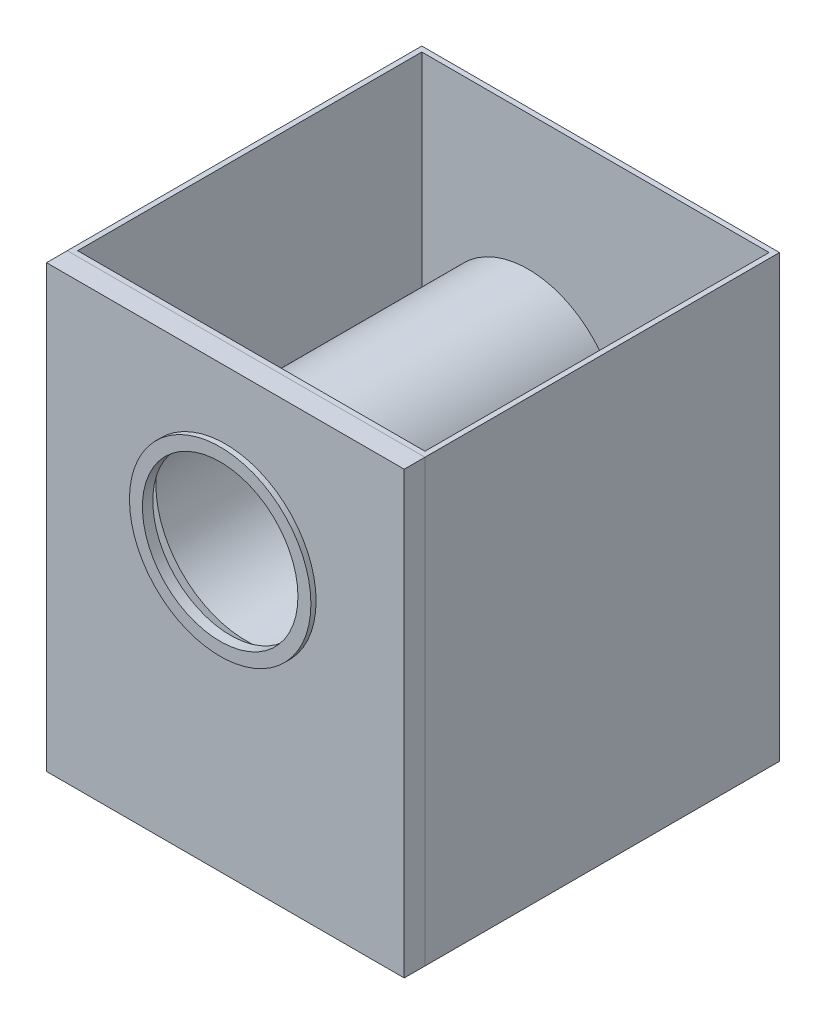
SolidWorks part; units mm, degrees
ref_plane "Front Plane" through (0, 0, 0) normal (0, 0, 1) x (1, 0, 0)
ref_plane "Top Plane" through (0, 0, 0) normal (0, 1, 0) x (1, 0, 0)
ref_plane "Right Plane" through (0, 0, 0) normal (1, 0, 0) x (0, 0, -1)
ref_plane "Plane1" through (0, -890, 0) normal (0, -1, 0) x (-1, 0, 0)
sketch "Sketch2" plane through (0, -890, 0) normal (0, -1, 0) x (-1, 0, 0)
  line L3 (-345, 361.95) -> (345, 361.95)
  line L4 (-345, 361.95) -> (-345, -321.95)
  line L5 (-345, -321.95) -> (345, -321.95)
  line L6 (345, 361.95) -> (345, -321.95)
  dimension "D1" = 683.9
  dimension "D2" = 690
extrude "Boss-Extrude2" add sketch "Sketch2" against normal blind 10
sketch "Sketch3" plane through (0, -890, 0) normal (0, -1, 0) x (-1, 0, 0)
  line L0 (335, 351.95) -> (335, -311.95)
  line L1 (345, 361.95) -> (-345, 361.95)
  line L2 (345, 361.95) -> (345, -321.95)
  line L3 (345, -321.95) -> (-345, -321.95)
  line L4 (-345, 361.95) -> (-345, -321.95)
  line L5 (335, -311.95) -> (-335, -311.95)
  line L6 (-335, 351.95) -> (-335, -311.95)
  line L7 (335, 351.95) -> (-335, 351.95)
  dimension "D1" = 683.9
  dimension "D2" = 690
  dimension "D3" = 10
extrude "Boss-Extrude3" add sketch "Sketch3" against normal blind 850
ref_plane "Plane2" through (0, 0, 321.95) normal (0, 0, 1) x (1, 0, 0)
sketch "Sketch4" plane through (0, 0, 321.95) normal (0, 0, 1) x (1, 0, 0)
  line L0 (0, -890) -> (0, -595.2) construction
  line L1 (345, -890) -> (-345, -890) construction
  line L2 (0, -40) -> (0, -100) construction
  line L3 (345, -40) -> (-345, -40) construction
  line L4 (0, -100) -> (0, -80) construction
  line L5 (-345, -80) -> (-345, -555.2) construction
  line L6 (-345, -40) -> (-345, -890) construction
  line L7 (-345, -317.6) -> (-305, -317.6) construction
  line L8 (345, -317.6) -> (305, -317.6) construction
  line L9 (345, -40) -> (345, -890) construction
  line L10 (0, -595.2) -> (0, -345.2) construction
  circle A0 centre (0, -345.2) radius 175
  dimension "D3" = 350
  dimension "D1" = 294.8
  dimension "D2" = 60
extrude "Cut-Extrude7" cut sketch "Sketch4" against normal blind 30
ref_plane "Plane3" through (0, 0, 361.95) normal (0, 0, 1) x (1, 0, 0)
sketch "Sketch5" plane through (0, 0, 361.95) normal (0, 0, 1) x (1, 0, 0)
  line L1 (-345, -40) -> (345, -40)
  line L2 (-345, -40) -> (-345, -890)
  line L3 (-345, -890) -> (345, -890)
  line L4 (345, -40) -> (345, -890)
  dimension "D1" = 850
  dimension "D2" = 690
extrude "Boss-Extrude4" add sketch "Sketch5" against normal blind 10 separate body
sketch "Sketch6" plane through (0, 0, 361.95) normal (0, 0, 1) x (1, 0, 0)
  circle A1 centre (0, -345.2) radius 175
  circle A2 centre (0, -345.2) radius 150
  dimension "D1" = 350
  dimension "D2" = 300
sketch "Sketch7" plane through (0, 0, 361.95) normal (0, 0, 1) x (1, 0, 0)
  line L1 (345, -40) -> (-345, -40)
  line L2 (345, -40) -> (345, -890)
  line L3 (345, -890) -> (-345, -890)
  line L4 (-345, -40) -> (-345, -890)
  line L6 (345, -890) -> (-345, -890) construction
  line L7 (-345, -40) -> (-345, -890) construction
  line L8 (344, -41) -> (344, -889)
  line L9 (344, -889) -> (-344, -889)
  line L10 (-344, -41) -> (-344, -889)
  line L11 (344, -41) -> (-344, -41)
  dimension "D1" = 850
  dimension "D2" = 690
  dimension "D3" = 1
extrude "Boss-Extrude5" add sketch "Sketch7" against normal blind 40
sketch "Sketch8" plane through (0, 0, 361.95) normal (0, 0, 1) x (1, 0, 0)
  line L1 (-345, -40) -> (345, -40)
  line L2 (-345, -40) -> (-345, -110)
  line L3 (-345, -110) -> (345, -110)
  line L4 (345, -40) -> (345, -110)
  line L5 (345, -890) -> (345, -40) construction
  dimension "D1" = 70
  dimension "D2" = 690
extrude "Boss-Extrude6" add sketch "Sketch6" along normal blind 10
sketch "Sketch9" plane through (0, 0, 321.95) normal (0, 0, 1) x (1, 0, 0)
  circle A0 centre (0, -345.2) radius 175
  circle A1 centre (0, -345.2) radius 174
  dimension "D1" = 350
  dimension "D2" = 1
extrude "Boss-Extrude8" add sketch "Sketch9" against normal blind 544
sketch "Sketch10" plane through (0, 0, 361.95) normal (0, 0, 1) x (1, 0, 0)
  circle A0 centre (0, -345.2) radius 150
  dimension "D1" = 300
extrude "Cut-Extrude8" cut sketch "Sketch10" against normal blind 50
